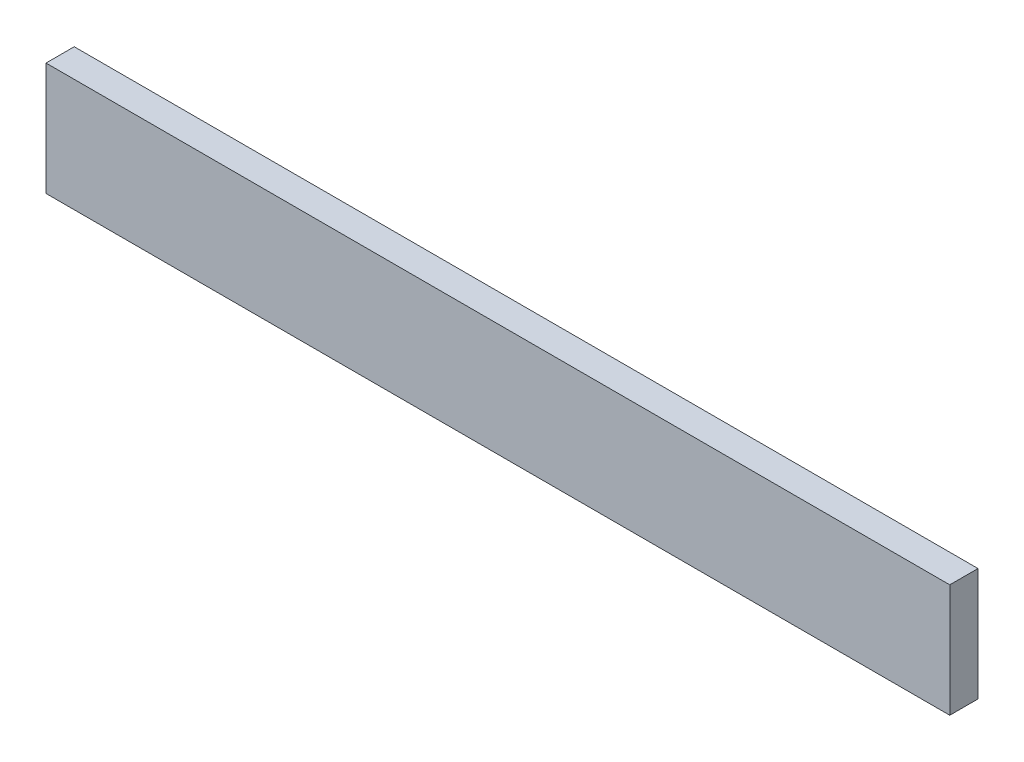
SolidWorks part; units mm, degrees
ref_plane "Front Plane" through (0, 0, 0) normal (0, 0, 1) x (1, 0, 0)
ref_plane "Top Plane" through (0, 0, 0) normal (0, 1, 0) x (1, 0, 0)
ref_plane "Right Plane" through (0, 0, 0) normal (1, 0, 0) x (0, 0, -1)
sketch "Sketch1" plane through (0, 0, 0) normal (0, 0, 1) x (1, 0, 0)
  line L1 (0, 0) -> (800, 0)
  line L2 (0, 0) -> (0, 100)
  line L3 (0, 100) -> (800, 100)
  line L4 (800, 0) -> (800, 100)
  dimension "D1" = 100
  dimension "D2" = 800
extrude "Boss-Extrude1" add sketch "Sketch1" along normal blind 25
